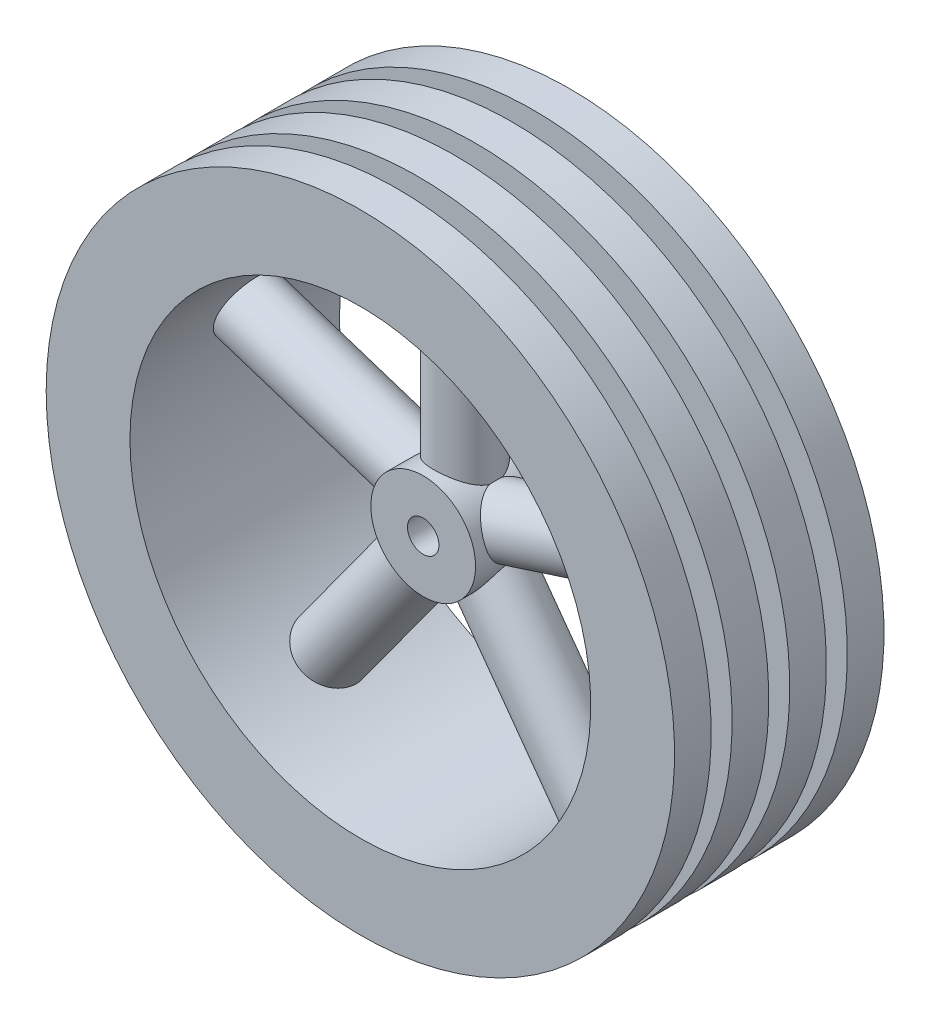
SolidWorks part; units mm, degrees
ref_plane "前基準面" through (0, 0, 0) normal (0, 0, 1) x (1, 0, 0)
ref_plane "上基準面" through (0, 0, 0) normal (0, 1, 0) x (1, 0, 0)
ref_plane "右基準面" through (0, 0, 0) normal (1, 0, 0) x (0, 0, -1)
sketch "草圖1" plane through (0, 0, 0) normal (0, 0, 1) x (1, 0, 0)
  circle A0 centre (0, 0) radius 1.5
  circle A1 centre (0, 0) radius 5
  dimension "D1" = 3
  dimension "D2" = 10
extrude "填料-伸長1" add sketch "草圖1" along normal blind 20
sketch "草圖2" plane through (0, 0, 0) normal (0, 1, 0) x (1, 0, 0)
  line L0 (-30, 0) -> (-22, 0)
  line L1 (-22, 0) -> (-22, -20)
  line L2 (-22, -20) -> (-30, -20)
  line L3 (-30, -20) -> (-30, -16.5)
  line L4 (-30, -16.5) -> (-25, -16.5)
  line L5 (-25, -16.5) -> (-25, -14.5)
  line L6 (-25, -14.5) -> (-30, -14.5)
  line L7 (-30, -14.5) -> (-30, -11)
  line L8 (-30, -11) -> (-25, -11)
  line L9 (-25, -11) -> (-25, -9)
  line L10 (-25, -9) -> (-30, -9)
  line L11 (-30, -9) -> (-30, -5.5)
  line L12 (-30, -5.5) -> (-25, -5.5)
  line L13 (-25, -5.5) -> (-25, -3.5)
  line L14 (-25, -3.5) -> (-30, -3.5)
  line L15 (-30, -3.5) -> (-30, 0)
  line L16 (0, 16.0606) -> (0, -28.2769) construction
  dimension "D1" = 2
  dimension "D2" = 2
  dimension "D3" = 2
  dimension "D4" = 20
  dimension "D5" = 3.5
  dimension "D6" = 3.5
  dimension "D7" = 3.5
  dimension "D8" = 30
  dimension "D9" = 30
  dimension "D10" = 30
  dimension "D11" = 25
  dimension "D12" = 25
  dimension "D13" = 25
  dimension "D14" = 30
  dimension "D15" = 22
ref_plane "平面1" through (0, 12, 0) normal (0, 1, 0) x (1, 0, 0)
revolve "旋轉2" add sketch "草圖2" angle 360 about L16
sketch "草圖5" plane through (0, 12, 0) normal (0, 1, 0) x (1, 0, 0)
  line L0 (0, 10.4043) -> (0, -26.7021) construction
  line L1 (5, 0) -> (-5, 0) construction
  circle A0 centre (0, -10) radius 3
  dimension "D1" = 6
  dimension "D2" = 10
extrude "填料-伸長2" add sketch "草圖5" along normal up to next and the other way up to next
pattern_circular "環狀複製排列1" count 5 over 360 about axis through (0, 0, 20) along (0, 0, -1) of "填料-伸長2"
sketch "草圖7" plane through (0, 0, 20) normal (0, 0, 1) x (1, 0, 0)
  circle A0 centre (0, 0) radius 5
  dimension "D1" = 10
extrude "除料-伸長1" cut sketch "草圖7" against normal blind 6
